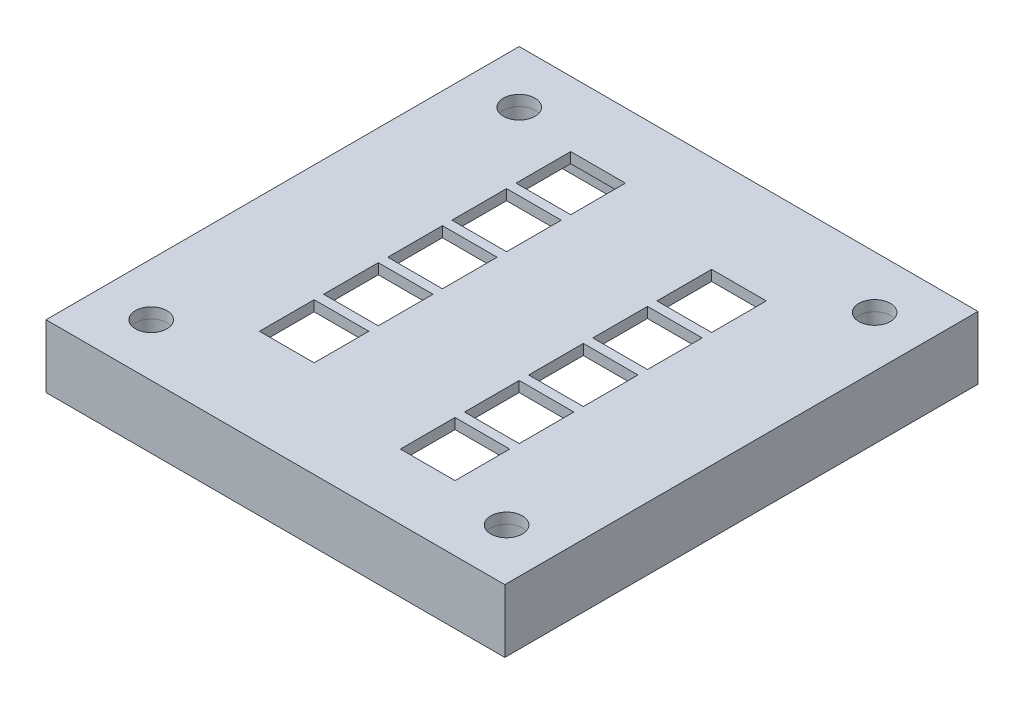
SolidWorks part; units mm, degrees
ref_plane "Спереди" through (0, 0, 0) normal (0, 0, 1) x (1, 0, 0)
ref_plane "Сверху" through (0, 0, 0) normal (0, 1, 0) x (1, 0, 0)
ref_plane "Справа" through (0, 0, 0) normal (1, 0, 0) x (0, 0, -1)
sketch "Эскиз1" plane through (0, 0, 0) normal (0, 1, 0) x (1, 0, 0)
  line L0 (-22.1709, -23.1183) -> (21.4607, -23.1183)
  line L1 (21.4607, -23.1183) -> (21.4607, 21.8817)
  line L2 (21.4607, 21.8817) -> (-22.1709, 21.8817)
  line L3 (-22.1709, 21.8817) -> (-22.1709, -23.1183)
  line L4 (-11.0709, 10.4817) -> (-5.8709, 10.4817)
  line L5 (-5.8709, 10.4817) -> (-5.8709, 15.6817)
  line L6 (-5.8709, 15.6817) -> (-11.0709, 15.6817)
  line L7 (-11.0709, 15.6817) -> (-11.0709, 10.4817)
  line L8 (-11.0709, 4.3817) -> (-5.8709, 4.3817)
  line L9 (-5.8709, 4.3817) -> (-5.8709, 9.5817)
  line L10 (-5.8709, 9.5817) -> (-11.0709, 9.5817)
  line L11 (-11.0709, 9.5817) -> (-11.0709, 4.3817)
  line L12 (-11.0709, -1.7183) -> (-5.8709, -1.7183)
  line L13 (-5.8709, -1.7183) -> (-5.8709, 3.4817)
  line L14 (-5.8709, 3.4817) -> (-11.0709, 3.4817)
  line L15 (-11.0709, 3.4817) -> (-11.0709, -1.7183)
  line L16 (-11.0709, -7.8183) -> (-5.8709, -7.8183)
  line L17 (-5.8709, -7.8183) -> (-5.8709, -2.6183)
  line L18 (-5.8709, -2.6183) -> (-11.0709, -2.6183)
  line L19 (-11.0709, -2.6183) -> (-11.0709, -7.8183)
  line L20 (-11.0709, -13.9186) -> (-5.8709, -13.9186)
  line L21 (-5.8709, -13.9186) -> (-5.8709, -8.7186)
  line L22 (-5.8709, -8.7186) -> (-11.0709, -8.7186)
  line L23 (-11.0709, -8.7186) -> (-11.0709, -13.9186)
  line L24 (5.3291, 7.4814) -> (10.5291, 7.4814)
  line L25 (10.5291, 7.4814) -> (10.5291, 12.6814)
  line L26 (10.5291, 12.6814) -> (5.3291, 12.6814)
  line L27 (5.3291, 12.6814) -> (5.3291, 7.4814)
  line L28 (5.3291, 1.3814) -> (10.5291, 1.3814)
  line L29 (10.5291, 1.3814) -> (10.5291, 6.5814)
  line L30 (10.5291, 6.5814) -> (5.3291, 6.5814)
  line L31 (5.3291, 6.5814) -> (5.3291, 1.3814)
  line L32 (5.3291, -4.7186) -> (10.5291, -4.7186)
  line L33 (10.5291, -4.7186) -> (10.5291, 0.4814)
  line L34 (10.5291, 0.4814) -> (5.3291, 0.4814)
  line L35 (5.3291, 0.4814) -> (5.3291, -4.7186)
  line L36 (5.3291, -10.8186) -> (10.5291, -10.8186)
  line L37 (10.5291, -10.8186) -> (10.5291, -5.6186)
  line L38 (10.5291, -5.6186) -> (5.3291, -5.6186)
  line L39 (5.3291, -5.6186) -> (5.3291, -10.8186)
  line L40 (5.3291, -16.9186) -> (10.5291, -16.9186)
  line L41 (10.5291, -16.9186) -> (10.5291, -11.7186)
  line L42 (10.5291, -11.7186) -> (5.3291, -11.7186)
  line L43 (5.3291, -11.7186) -> (5.3291, -16.9186)
  ellipse E0 centre (-17.1709, 16.8817) end of major axis (-17.1709, 18.3817) minor radius 1.5
  ellipse E1 centre (-17.1709, -18.1183) end of major axis (-17.1709, -16.6183) minor radius 1.5
  ellipse E2 centre (16.6291, 16.8817) end of major axis (16.6291, 18.3817) minor radius 1.5
  ellipse E3 centre (16.6291, -18.1183) end of major axis (16.6291, -16.6183) minor radius 1.5
  dimension "D1" = 45
extrude "Бобышка-Вытянуть1" add sketch "Эскиз1" along normal blind 1
sketch "Эскиз3" plane through (0, 0, 0) normal (0, -1, 0) x (1, 0, 0)
  circle A0 centre (-17.1709, 18.1183) radius 1.5
  circle A1 centre (-17.1709, 18.1183) radius 4
  circle A2 centre (16.6291, 18.1183) radius 1.5
  circle A3 centre (16.6291, 18.1183) radius 4
  circle A4 centre (-17.1709, -16.8817) radius 1.5
  circle A5 centre (-17.1709, -16.8817) radius 4
  circle A6 centre (16.6291, -16.8817) radius 1.5
  circle A7 centre (16.6291, -16.8817) radius 4
  dimension "D1" = 3
  dimension "D2" = 8
extrude "Бобышка-Вытянуть3" add sketch "Эскиз3" along normal blind 1.2
sketch "Эскиз4" plane through (0, 0, 0) normal (0, -1, 0) x (1, 0, 0)
  line L1 (-22.1709, -21.8817) -> (21.4607, -21.8817)
  line L2 (-22.1709, -21.8817) -> (-22.1709, 23.1183)
  line L3 (-22.1709, 23.1183) -> (21.4607, 23.1183)
  line L4 (21.4607, -21.8817) -> (21.4607, 23.1183)
  line L5 (-20.1709, -19.8817) -> (19.4607, -19.8817)
  line L6 (-20.1709, -19.8817) -> (-20.1709, 21.1183)
  line L7 (-20.1709, 21.1183) -> (19.4607, 21.1183)
  line L8 (19.4607, -19.8817) -> (19.4607, 21.1183)
  dimension "D1" = 2
  dimension "D2" = 2
  dimension "D3" = 2
  dimension "D4" = 2
extrude "Бобышка-Вытянуть4" add sketch "Эскиз4" along normal blind 5
sketch "Эскиз5" plane through (0, -5, 0) normal (0, -1, 0) x (1, 0, 0)
  line L0 (-20.1709, 21.1183) -> (-20.1709, -19.8817) construction
  line L1 (-20.1709, 13.1183) -> (-22.1709, 13.1183)
  line L2 (-20.1709, 13.1183) -> (-20.1709, -11.8817)
  line L3 (-20.1709, -11.8817) -> (-22.1709, -11.8817)
  line L4 (-22.1709, 13.1183) -> (-22.1709, -11.8817)
  line L5 (-22.1709, 23.1183) -> (-22.1709, -21.8817) construction
  line L6 (-22.1709, -21.8817) -> (21.4607, -21.8817) construction
  line L7 (21.4607, 23.1183) -> (-22.1709, 23.1183) construction
  dimension "D1" = 10
  dimension "D2" = 10
extrude "Вырез-Вытянуть1" cut sketch "Эскиз5" against normal blind 5
